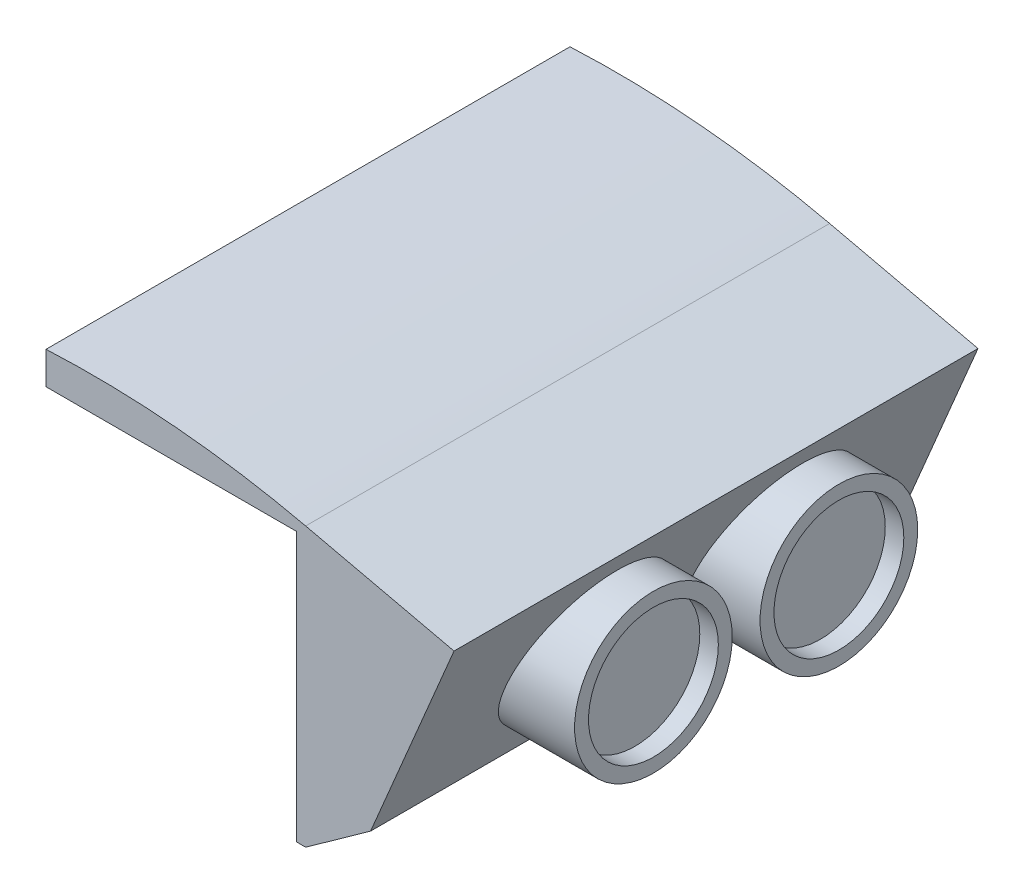
SolidWorks part; units mm, degrees
ref_plane "Front Plane" through (0, 0, 0) normal (0, 0, 1) x (1, 0, 0)
ref_plane "Top Plane" through (0, 0, 0) normal (0, 1, 0) x (1, 0, 0)
ref_plane "Right Plane" through (0, 0, 0) normal (1, 0, 0) x (0, 0, -1)
sketch "Sketch1" plane through (0, 0, 0) normal (0, 1, 0) x (1, 0, 0)
  line L0 (-14, 28.25) -> (14, 28.25)
  line L1 (14, 28.25) -> (14, -28.25)
  line L2 (-14, 28.25) -> (-14, -28.25)
  line L3 (-14, -28.25) -> (14, -28.25)
  point P6 (-14, 0)
  point P7 (0, 28.25)
  dimension "D1" = 56.5
  dimension "D2" = 28
extrude "Boss-Extrude1" add sketch "Sketch1" against normal blind 30 contours L0 L1 L3 L2
sketch "Sketch5" plane through (0, 0, -28.25) normal (0, 0, -1) x (-1, 0, 0)
  line L0 (-1, -30) -> (-1, -26)
  line L1 (14, -30) -> (-14, -30) construction
  line L2 (14, -30) -> (14, 0) construction
  line L3 (-1, -30) -> (14, -30)
  line L4 (14, -30) -> (14, -6.6351)
  arc A0 (-1, -26) -> (14, -6.6351) centre (19, -26) cw
  dimension "D1" = 20
  dimension "D2" = 4
  dimension "D3" = 15
extrude "Cut-Extrude2" cut sketch "Sketch5" against normal up to surface (56.5 mm away) contours A0 L4 L3 L0 up to face at (0, -15, 28.25)
shell "Shell1" thickness 1
ref_plane "Plane1" through (0, 0, -20) normal (0, 0, 1) x (1, 0, 0)
sketch "Sketch3" plane through (0, 0, -20) normal (0, 0, 1) x (1, 0, 0)
  line L0 (-14, -1) -> (-15, -1)
  line L1 (-14, -2) -> (-15, -2)
  line L2 (-14, -6.6351) -> (-14, 0) construction
  line L3 (-14, -2) -> (-12.5, -1)
  line L4 (-14, -1) -> (13, -1) construction
  line L5 (-12.5, -1) -> (-14, -1)
  arc A0 (-15, -1) -> (-15, -2) centre (-15, -1.5) ccw
  dimension "D2" = 0.5
  dimension "D1" = 1
  dimension "D3" = 1.5
extrude "Boss-Extrude3" add sketch "Sketch3" along normal mid plane 5 contours A0 L1 L3 L5 L0
sketch "Sketch4" plane through (0, 0, -22.5) normal (0, 0, -1) x (-1, 0, 0)
  circle A0 centre (15, -1.5) radius 0.35
  arc A1 (15, -2) -> (15, -1) centre (15, -1.5) ccw construction
  dimension "D1" = 0.15
extrude "Cut-Extrude1" cut sketch "Sketch4" against normal up to surface (5 mm away) up to face at (-14.2, -1.4, -17.5)
mirror "Mirror1" about plane through (0, 0, 0) normal (0, 0, 1) of "Cut-Extrude1", "Boss-Extrude3"
sketch "Sketch6" plane through (0, 0, -28.25) normal (0, 0, -1) x (-1, 0, 0)
  line L0 (14, 0) -> (14, 2.5)
  line L1 (-14, 0) -> (-30, -3.6778)
  line L2 (-30, -3.6778) -> (-21, -25)
  line L3 (-21, -25) -> (-14, -30)
  line L4 (14, -6.6351) -> (14, 0) construction
  line L5 (14, 0) -> (-14, 0) construction
  line L6 (-14, -30) -> (-14, 0)
  line L7 (14, 0) -> (-14, 0)
  arc A0 (14, 2.5) -> (-14, 0) centre (9.0743, -100.3822) ccw
  line M3 (14, 0) -> (-14, 0)
  line M4 (-14, 0) -> (-14, -30)
  dimension "D2" = 103
  dimension "D1" = 2.5
  dimension "D3" = 35
  dimension "D4" = 44
  dimension "D5" = 25
extrude "Boss-Extrude4" add sketch "Sketch6" against normal up to surface (56.5 mm away) contours L2 L3 L1 M4 | L0 A0 M3 up to face at (4.3333, -10.3333, 28.25)
ref_plane "Plane2" through (33, 0, 0) normal (1, 0, 0) x (0, 0, -1)
sketch "Sketch7" plane through (33, 0, 0) normal (1, 0, 0) x (0, 0, -1)
  line L0 (-28.25, -3.6778) -> (-28.25, -25) construction
  line L1 (28.25, -3.6778) -> (28.25, -25) construction
  circle A0 centre (10.25, -14.3389) radius 8.5
  point P2 (-28.25, -14.3389)
  dimension "D2" = 17
  dimension "D1" = 18
extrude "Boss-Extrude5" add sketch "Sketch7" against normal up to surface (7.5 mm away)
sketch "Sketch8" plane through (33, 0, 0) normal (1, 0, 0) x (0, 0, -1)
  circle A0 centre (10.25, -14.3389) radius 7
  circle A1 centre (10.25, -14.3389) radius 8.5 construction
  dimension "D1" = 1.5
extrude "Cut-Extrude3" cut sketch "Sketch8" against normal blind 2
pattern_linear "LPattern1" count 2 spacing 20 along (0, 0, 1) of "Boss-Extrude5", "Cut-Extrude3"
